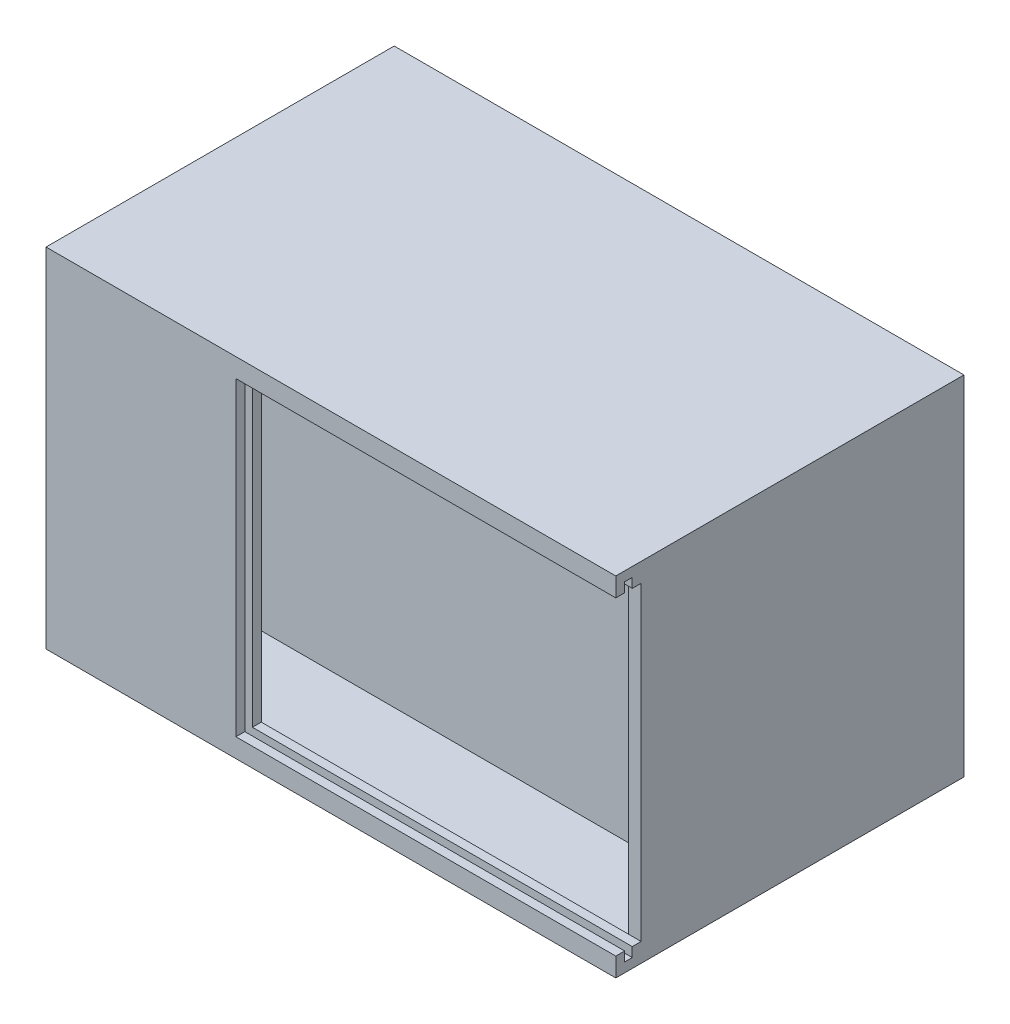
SolidWorks part; units mm, degrees
ref_plane "Front Plane" through (0, 0, 0) normal (0, 0, 1) x (1, 0, 0)
ref_plane "Top Plane" through (0, 0, 0) normal (0, 1, 0) x (1, 0, 0)
ref_plane "Right Plane" through (0, 0, 0) normal (1, 0, 0) x (0, 0, -1)
sketch "Sketch1" plane through (0, 0, 0) normal (0, 0, 1) x (1, 0, 0)
  line L1 (-45, 27.5) -> (45, 27.5)
  line L2 (-45, 27.5) -> (-45, -27.5)
  line L3 (-45, -27.5) -> (45, -27.5)
  line L4 (45, 27.5) -> (45, -27.5)
  line L5 (-45, 27.5) -> (45, -27.5) construction
  line L6 (-45, -27.5) -> (45, 27.5) construction
  point P0 (0, 0)
  dimension "D1" = 90
  dimension "D2" = 55
extrude "Boss-Extrude1" add sketch "Sketch1" along normal blind 55
shell "Shell1" thickness 2
sketch "Sketch2" plane through (45, 0, 0) normal (1, 0, 0) x (0, 0, -1)
  line L0 (-55, -27.5) -> (0, -27.5) construction
  line L11 (-55, 27.5) -> (-51, 27.5)
  line L12 (-55, 27.5) -> (-55, -27.5)
  line L13 (-55, -27.5) -> (-51, -27.5)
  line L14 (-51, 27.5) -> (-51, -27.5)
  dimension "D1" = 4
extrude "Boss-Extrude2" add sketch "Sketch2" against normal up to surface (88 mm away) up to face at (-43, 0, 28.5)
sketch "Sketch3" plane through (45, 0, 0) normal (1, 0, 0) x (0, 0, -1)
  line L0 (-55, -27.5) -> (-55, 27.5) construction
  line L1 (-55, 24.5) -> (-51, 24.5)
  line L2 (-55, 24.5) -> (-55, -24.5)
  line L3 (-55, -24.5) -> (-51, -24.5)
  line L4 (-51, 24.5) -> (-51, -24.5)
  line L5 (-55, 27.5) -> (0, 27.5) construction
  line L6 (-55, -27.5) -> (0, -27.5) construction
  dimension "D1" = 4
  dimension "D2" = 3
  dimension "D3" = 3
extrude "Cut-Extrude1" cut sketch "Sketch3" against normal blind 60
sketch "Sketch4" plane through (45, 0, 0) normal (1, 0, 0) x (0, 0, -1)
  line L0 (-55, -27.5) -> (0, -27.5) construction
  line L1 (-53.6, 26) -> (-52.4, 26)
  line L2 (-53.6, 26) -> (-53.6, -26)
  line L3 (-53.6, -26) -> (-52.4, -26)
  line L4 (-52.4, 26) -> (-52.4, -26)
  line L5 (-55, 27.5) -> (0, 27.5) construction
  line L6 (-55, -27.5) -> (-55, -24.5) construction
  dimension "D1" = 1.5
  dimension "D2" = 1.5
  dimension "D3" = 1.4
  dimension "D4" = 1.2
extrude "Cut-Extrude2" cut sketch "Sketch4" against normal blind 61.5
sketch "Sketch5" plane through (0, 0, 55) normal (0, 0, 1) x (1, 0, 0)
  line L0 (-45, 27.5) -> (-45, -27.5) construction
  line L1 (-39, 9.5) -> (-26, 9.5)
  line L2 (-39, 9.5) -> (-39, -10)
  line L3 (-39, -10) -> (-26, -10)
  line L4 (-26, 9.5) -> (-26, -10)
  line L5 (-45, -27.5) -> (45, -27.5) construction
  dimension "D1" = 13
  dimension "D2" = 19.5
  dimension "D3" = 6
  dimension "D4" = 17.5
extrude "Cut-Extrude3" cut sketch "Sketch5" against normal through all from offset 10 offset against normal yes
sketch "Sketch7" plane through (0, 0, 2) normal (0, 0, 1) x (1, 0, 0)
  line L0 (-43, 25.5) -> (-43, -25.5) construction
  line L3 (43, 25.5) -> (-43, 25.5) construction
  circle A0 centre (3, 19.5) radius 5
  circle A1 centre (-13, -9) radius 5
  circle A2 centre (13, 17.5) radius 5
  circle A3 centre (37, -6.5) radius 5
  dimension "D1" = 10
  dimension "D3" = 10
  dimension "D6" = 10
  dimension "D8" = 10
  dimension "D2" = 6
  dimension "D4" = 28.5
  dimension "D5" = 16
  dimension "D7" = 8
  dimension "D9" = 24
  dimension "D10" = 24
  dimension "D11" = 10
  dimension "D12" = 30
extrude "Boss-Extrude3" add sketch "Sketch7" along normal blind 5
sketch "Sketch8" plane through (0, 0, 7) normal (0, 0, 1) x (1, 0, 0)
  circle A0 centre (13, 17.5) radius 1.4
  circle A1 centre (-13, -9) radius 1.4
  circle A2 centre (37, -6.5) radius 1.4
  circle A3 centre (3, 19.5) radius 1.4
  circle A4 centre (3, 19.5) radius 5 construction
  circle A5 centre (-13, -9) radius 5 construction
  circle A6 centre (37, -6.5) radius 5 construction
  dimension "D1" = 2.8
  dimension "D2" = 2.8
  dimension "D3" = 2.8
  dimension "D4" = 2.8
  dimension "D5" = 0
  dimension "D6" = 0
  dimension "D7" = 0
extrude "Cut-Extrude4" cut sketch "Sketch8" against normal blind 5
sketch "Sketch9" plane through (-43, 0, 0) normal (1, 0, 0) x (0, 0, -1)
  line L0 (-51, 25.5) -> (-2, 25.5) construction
  line L1 (-33.5, 25.5) -> (-37.5, 25.5)
  line L2 (-33.5, 25.5) -> (-33.5, -25.5)
  line L3 (-33.5, -25.5) -> (-37.5, -25.5)
  line L4 (-37.5, 25.5) -> (-37.5, -25.5)
  line L6 (-51, 25.5) -> (-51, -25.5) construction
  dimension "D1" = 13.5
  dimension "D2" = 4
extrude "Boss-Extrude4" add sketch "Sketch9" along normal up to next
sketch "Sketch11" plane through (0, -25.5, 0) normal (0, 1, 0) x (1, 0, 0)
  line L0 (43, -37.5) -> (-43, -37.5) construction
  line L1 (8, -33.5) -> (43, -33.5)
  line L2 (8, -33.5) -> (8, -37.5)
  line L3 (8, -37.5) -> (43, -37.5)
  line L4 (43, -33.5) -> (43, -37.5)
  line L5 (43, -51) -> (43, -37.5) construction
  dimension "D1" = 0
  dimension "D2" = 4
  dimension "D3" = 0
  dimension "D4" = 35
extrude "Boss-Extrude5" [suppressed] add sketch "Sketch11" along normal blind 18
sketch "Sketch12" [suppressed] plane through (0, 0, 37.5) normal (0, 0, 1) x (1, 0, 0)
  line L1 (43, -7.5) -> (31.7234, -7.5)
  line L2 (43, -7.5) -> (43, -11.3823)
  line L3 (43, -11.3823) -> (31.7234, -11.3823)
  line L4 (31.7234, -7.5) -> (31.7234, -11.3823)
extrude "Cut-Extrude5" [suppressed] cut sketch "Sketch12" against normal up to next
